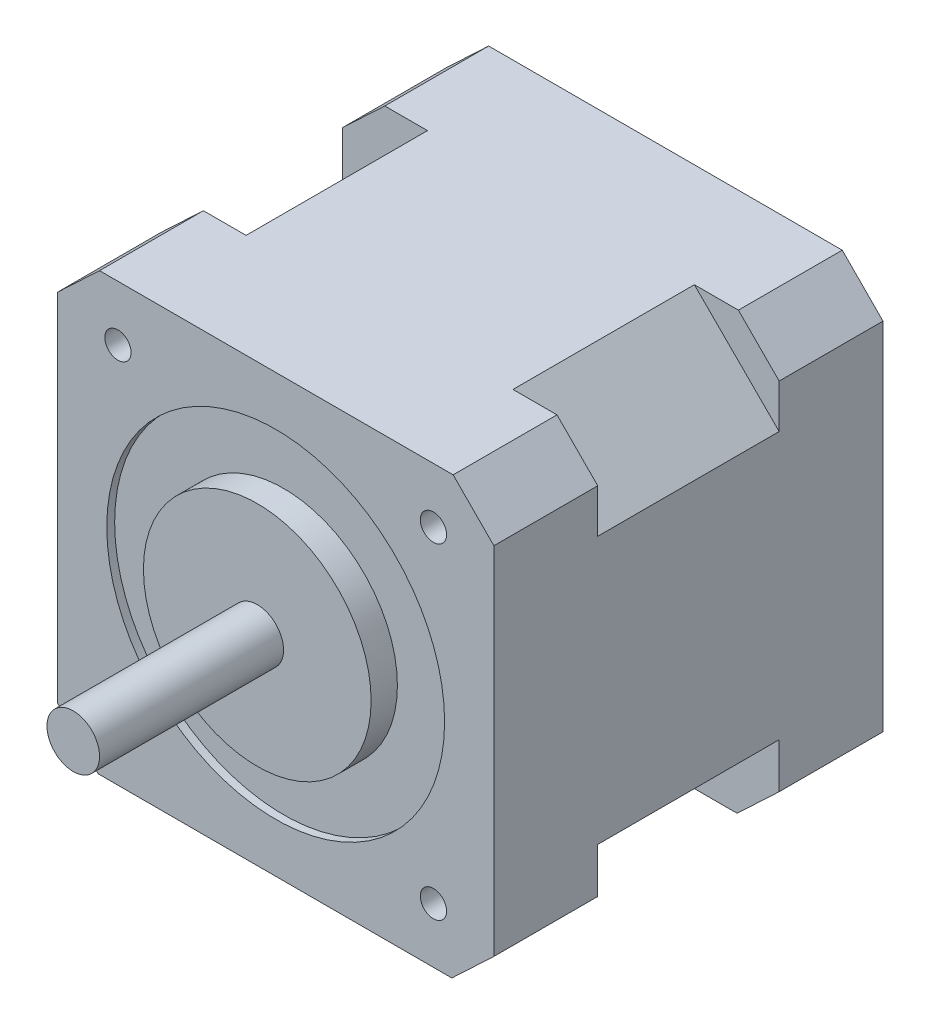
SolidWorks part; units mm, degrees
ref_plane "Front Plane" through (0, 0, 0) normal (0, 0, 1) x (1, 0, 0)
ref_plane "Top Plane" through (0, 0, 0) normal (0, 1, 0) x (1, 0, 0)
ref_plane "Right Plane" through (0, 0, 0) normal (1, 0, 0) x (0, 0, -1)
sketch "Sketch1" plane through (0, 0, 0) normal (0, 0, 1) x (1, 0, 0)
  line L0 (-21.082, 17.2467) -> (-17.018, 21.082)
  line L1 (-17.018, 21.082) -> (17.145, 21.082)
  line L2 (-21.082, 17.2467) -> (-21.082, -17.1164)
  line L3 (-17.145, -21.082) -> (17.018, -21.082)
  line L4 (21.082, 17.1164) -> (21.082, -17.2467)
  line L5 (-21.082, 21.082) -> (21.082, -21.082) construction
  line L6 (-21.082, -21.082) -> (21.082, 21.082) construction
  line L7 (17.145, 21.082) -> (21.082, 17.1164)
  line L8 (17.018, -21.082) -> (21.082, -17.2467)
  line L9 (-21.082, -17.1164) -> (-17.145, -21.082)
  point P0 (0, 0)
  dimension "D1" = 42.164
  dimension "D4" = 42.164
  dimension "D5" = 3.937
  dimension "D6" = 3.9656
  dimension "D3" = 5.588
  dimension "D2" = 5.588
  dimension "D7" = 4.064
  dimension "D8" = 3.9656
extrude "Boss-Extrude1" add sketch "Sketch1" against normal blind 10.033
sketch "Sketch2" plane through (0, 0, -10.033) normal (0, 0, -1) x (-1, 0, 0)
  line L0 (-21.082, 12.892) -> (-12.892, 21.082)
  line L1 (-21.082, -17.2467) -> (-21.082, 17.1164) construction
  line L2 (-17.145, 21.082) -> (17.018, 21.082) construction
  line L3 (-12.892, 21.082) -> (12.892, 21.082)
  line L4 (12.892, 21.082) -> (21.082, 12.892)
  line L5 (21.082, 17.2467) -> (21.082, -17.1164) construction
  line L6 (21.082, 12.892) -> (21.082, -12.892)
  line L7 (21.082, -12.892) -> (12.892, -21.082)
  line L8 (17.145, -21.082) -> (-17.018, -21.082) construction
  line L9 (12.892, -21.082) -> (-12.892, -21.082)
  line L10 (-12.892, -21.082) -> (-21.082, -12.892)
  line L11 (-21.082, -12.892) -> (-21.082, 12.892)
  dimension "D1" = 11.5824
  dimension "D2" = 11.5824
  dimension "D3" = 11.5824
extrude "Boss-Extrude2" add sketch "Sketch2" along normal blind 18.034
ref_plane "Plane1" through (0, 0, -18.796) normal (0, 0, 1) x (1, 0, 0)
mirror "Mirror2" about plane through (0, 0, -18.796) normal (0, 0, 1) of "Boss-Extrude1"
sketch "Sketch3" plane through (0, 0, 0) normal (0, 0, 1) x (1, 0, 0)
  circle A0 centre (0, 0) radius 16.3195
  dimension "D1" = 32.639
extrude "Cut-Extrude1" cut sketch "Sketch3" against normal blind 0.762
sketch "Sketch4" plane through (0, 0, -0.762) normal (0, 0, 1) x (1, 0, 0)
  circle A0 centre (0, 0) radius 10.9982
  dimension "D1" = 21.9964
extrude "Boss-Extrude3" add sketch "Sketch4" along normal blind 2.54
sketch "Sketch5" plane through (0, 0, 1.778) normal (0, 0, 1) x (1, 0, 0)
  circle A0 centre (0, 0) radius 2.54
  dimension "D1" = 5.08
extrude "Boss-Extrude4" add sketch "Sketch5" along normal blind 17.78
sketch "Sketch6" plane through (0, 0, 0) normal (0, 0, 1) x (1, 0, 0)
  line L0 (17.145, 21.082) -> (-17.018, 21.082) construction
  circle A0 centre (-15.24, 15.748) radius 1.27
  circle A1 centre (15.24, 15.748) radius 1.27
  dimension "D1" = 2.54
  dimension "D2" = 2.54
  dimension "D3" = 30.48
  dimension "D4" = 15.24
  dimension "D5" = 5.334
extrude "Cut-Extrude2" cut sketch "Sketch6" against normal blind 7.62
mirror "Mirror3" about plane through (0, 0, 0) normal (0, 1, 0) of "Cut-Extrude2"
